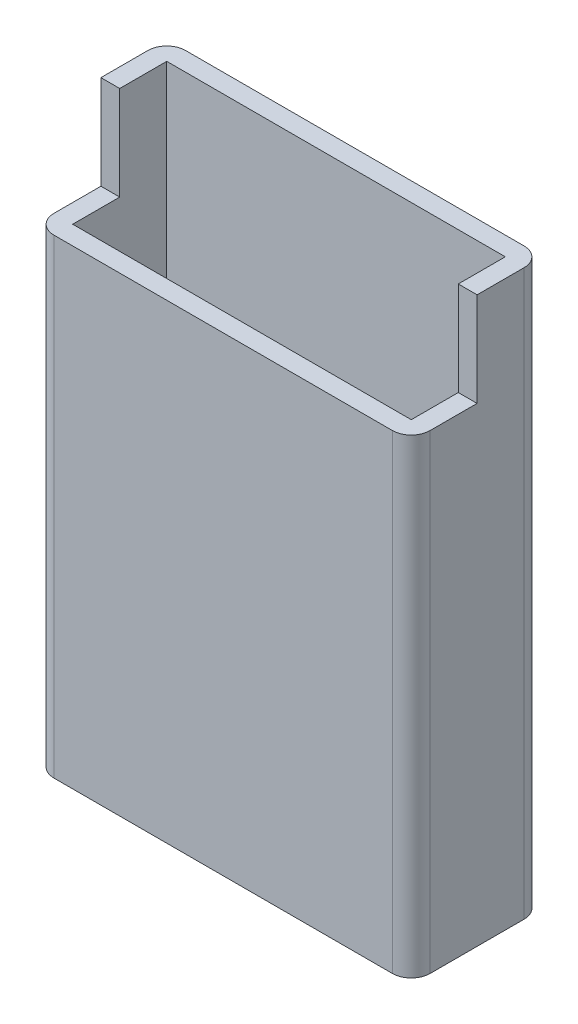
SolidWorks part; units mm, degrees
ref_plane "前视基准面" through (0, 0, 0) normal (0, 0, 1) x (1, 0, 0)
ref_plane "上视基准面" through (0, 0, 0) normal (0, 1, 0) x (1, 0, 0)
ref_plane "右视基准面" through (0, 0, 0) normal (1, 0, 0) x (0, 0, -1)
sketch "草图1" plane through (0, 0, 0) normal (0, 1, 0) x (1, 0, 0)
  line L1 (0, 14) -> (40, 14)
  line L2 (0, 14) -> (0, 0)
  line L3 (0, 0) -> (40, 0)
  line L4 (40, 14) -> (40, 0)
extrude "凸台-拉伸1" add sketch "草图1" along normal blind 60 contours L1 L4 L3 L2
sketch "草图6" plane through (0, 60, 0) normal (0, 1, 0) x (1, 0, 0)
  line L1 (2, 2) -> (38, 2)
  line L2 (2, 2) -> (2, 12)
  line L3 (2, 12) -> (38, 12)
  line L4 (38, 2) -> (38, 12)
extrude "切除-拉伸2" cut sketch "草图6" against normal blind 55 contours L3 L4 L1 L2
sketch "草图7" plane through (0, 0, 0) normal (0, 0, 1) x (1, 0, 0)
  line L0 (40, 60) -> (40, 0) construction
  line L1 (0, 60) -> (40, 60)
  line L2 (0, 60) -> (0, 50)
  line L3 (0, 50) -> (40, 50)
  line L4 (40, 60) -> (40, 50)
extrude "切除-拉伸3" cut sketch "草图7" against normal blind 7
sketch "草图15" plane through (0, 0, 0) normal (0, -1, 0) x (1, 0, 0)
  line L1 (2, -14) -> (38, -14)
  line L2 (0, -12) -> (0, -2)
  line L3 (2, 0) -> (38, 0)
  line L4 (40, -12) -> (40, -2)
  arc A0 (38, -14) -> (40, -12) centre (38, -12) ccw
  arc A1 (38, 0) -> (40, -2) centre (38, -2) cw
  arc A2 (2, -14) -> (0, -12) centre (2, -12) cw
  arc A3 (0, -2) -> (2, 0) centre (2, -2) cw
  point P10 (40, 0)
  point P13 (0, -14)
  dimension "D1" = 2
extrude "切除-拉伸5" cut sketch "草图15" against normal through all flip side to cut
